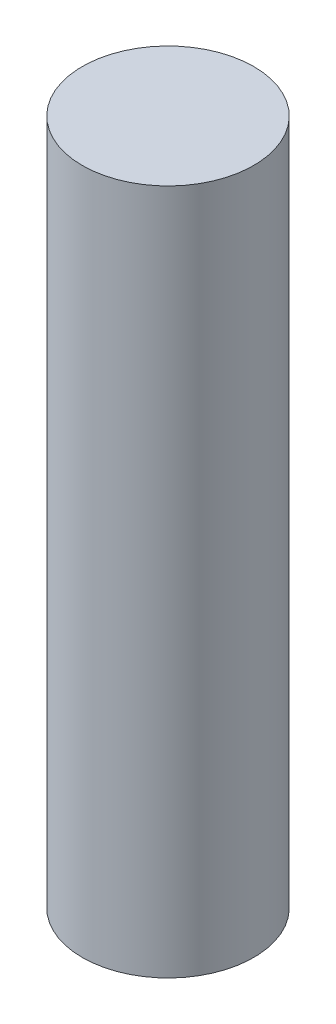
SolidWorks part; units mm, degrees
ref_plane "Face" through (0, 0, 0) normal (0, 0, 1) x (1, 0, 0)
ref_plane "Dessus" through (0, 0, 0) normal (0, 1, 0) x (1, 0, 0)
ref_plane "Droite" through (0, 0, 0) normal (1, 0, 0) x (0, 0, -1)
sketch "Esquisse1" plane through (0, 0, 0) normal (0, 1, 0) x (1, 0, 0)
  circle A0 centre (0, 0) radius 2
  dimension "D1" = 4
extrude "Extrusion1" add sketch "Esquisse1" along normal blind 16
